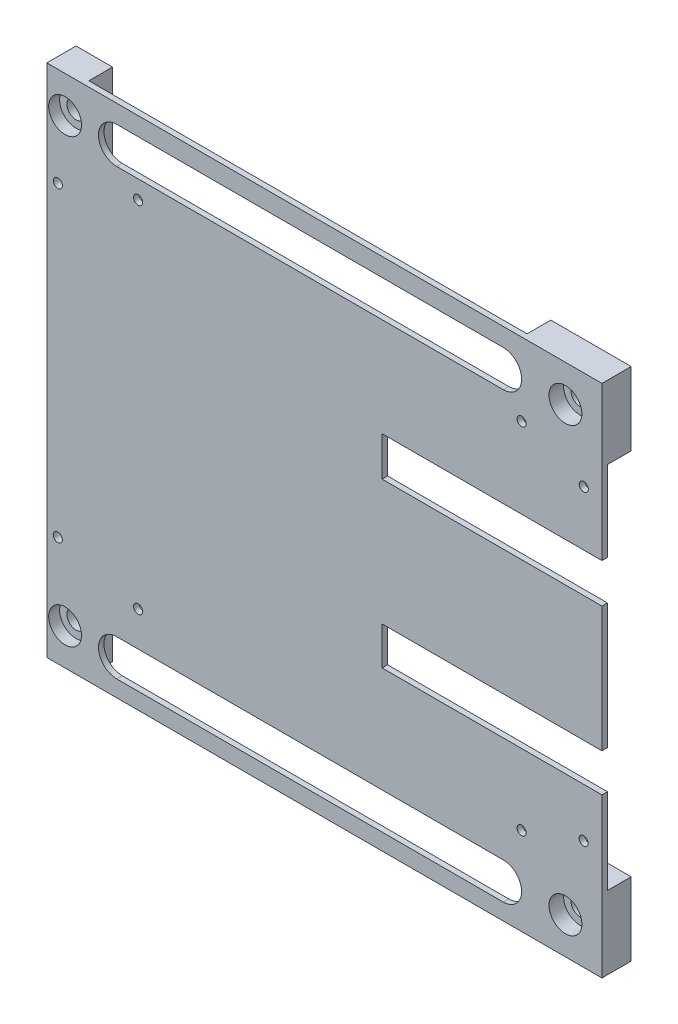
SolidWorks part; units mm, degrees
ref_plane "Front Plane" through (0, 0, 0) normal (0, 0, 1) x (1, 0, 0)
ref_plane "Top Plane" through (0, 0, 0) normal (0, 1, 0) x (1, 0, 0)
ref_plane "Right Plane" through (0, 0, 0) normal (1, 0, 0) x (0, 0, -1)
sketch "Sketch1" plane through (0, 0, 0) normal (0, 0, 1) x (1, 0, 0)
  line L0 (0, 0) -> (0, 141)
  line L1 (0, 141) -> (10, 141)
  line L2 (10, 141) -> (10, 0)
  line L3 (10, 0) -> (0, 0)
extrude "Boss-Extrude1" add sketch "Sketch1" along normal blind 8
sketch "Sketch2" plane through (0, 0, 8) normal (0, 0, 1) x (1, 0, 0)
  circle A0 centre (5, 131) radius 2.5
  circle A1 centre (5, 10) radius 2.5
extrude "Cut-Extrude1" cut sketch "Sketch2" against normal blind 8
sketch "Sketch3" plane through (0, 0, 8) normal (0, 0, 1) x (1, 0, 0)
  line L1 (10, 141) -> (152, 141)
  line L2 (10, 141) -> (10, 0)
  line L3 (10, 0) -> (152, 0)
  line L4 (152, 141) -> (152, 0)
extrude "Boss-Extrude2" add sketch "Sketch3" against normal blind 1.5
sketch "Sketch8" plane through (0, 0, 8) normal (0, 0, 1) x (1, 0, 0)
  line L0 (19.1432, 131) -> (125, 131) construction
  line L1 (19.1432, 136) -> (125, 136)
  line L2 (19.1432, 126) -> (125, 126)
  line L3 (19.1432, 9.4959) -> (125, 9.4959) construction
  line L4 (19.1432, 14.4959) -> (125, 14.4959)
  line L5 (19.1432, 4.4959) -> (125, 4.4959)
  arc A0 (19.1432, 136) -> (19.1432, 126) centre (19.1432, 131) ccw
  arc A1 (125, 126) -> (125, 136) centre (125, 131) ccw
  arc A2 (19.1432, 14.4959) -> (19.1432, 4.4959) centre (19.1432, 9.4959) ccw
  arc A3 (125, 4.4959) -> (125, 14.4959) centre (125, 9.4959) ccw
  point P3 (72.0716, 131)
  point P8 (125, 131)
  point P9 (0, 0)
  point P13 (72.0716, 9.4959)
  point P21 (0, 0)
  point P22 (125, 9.8292)
extrude "Cut-Extrude4" cut sketch "Sketch8" against normal blind 24
sketch "Sketch9" plane through (0, 0, 8) normal (0, 0, 1) x (1, 0, 0)
  circle A3 centre (147.0288, 114.0076) radius 1.25
  circle A4 centre (3.0274, 114) radius 1.25
  circle A5 centre (3, 30.0194) radius 1.25
  circle A6 centre (147, 30.0194) radius 1.25
sketch "Sketch12" plane through (0, 0, 8) normal (0, 0, 1) x (1, 0, 0)
  line L0 (151.8, -119) -> (151.8, 141) construction
  line L1 (151.8, 98.9737) -> (91.8, 98.9737)
  line L2 (151.8, 98.9737) -> (151.8, 88.196)
  line L3 (151.8, 88.196) -> (91.8, 88.196)
  line L4 (91.8, 98.9737) -> (91.8, 88.196)
  line L6 (151.8, 53.8659) -> (91.8, 53.8659)
  line L7 (151.8, 53.8659) -> (151.8, 43.4296)
  line L8 (151.8, 43.4296) -> (91.8, 43.4296)
  line L9 (91.8, 53.8659) -> (91.8, 43.4296)
  point P10 (0, 0)
  point P11 (0, 0)
extrude "Cut-Extrude6" cut sketch "Sketch12" against normal blind 10
sketch "Sketch13" plane through (0, 0, 8) normal (0, 0, 1) x (1, 0, 0)
  circle A0 centre (142, 131) radius 2.5
  circle A1 centre (142, 10) radius 2.5
sketch "Sketch14" plane through (0, 0, 6.5) normal (0, 0, -1) x (-1, 0, 0)
  line L1 (-152, 141) -> (-130, 141)
  line L2 (-152, 141) -> (-152, 121)
  line L3 (-152, 121) -> (-130, 121)
  line L4 (-130, 141) -> (-130, 121)
  line L5 (-152, 0) -> (-130, 0)
  line L6 (-152, 0) -> (-152, 20)
  line L7 (-152, 20) -> (-130, 20)
  line L8 (-130, 0) -> (-130, 20)
extrude "Boss-Extrude5" add sketch "Sketch14" along normal blind 6.5
sketch "Sketch16" plane through (0, 0, 8) normal (0, 0, 1) x (1, 0, 0)
  line L1 (91.8, 98.9737) -> (153.1804, 98.9737)
  line L2 (91.8, 98.9737) -> (91.8, 88.196)
  line L3 (91.8, 88.196) -> (153.1804, 88.196)
  line L4 (153.1804, 98.9737) -> (153.1804, 88.196)
  line L5 (91.8, 53.8659) -> (153.1804, 53.8659)
  line L6 (91.8, 53.8659) -> (91.8, 43.425)
  line L7 (91.8, 43.425) -> (153.1804, 43.425)
  line L8 (153.1804, 53.8659) -> (153.1804, 43.425)
extrude "Cut-Extrude9" cut sketch "Sketch16" against normal blind 26.5
sketch "Sketch17" plane through (0, 0, 8) normal (0, 0, 1) x (1, 0, 0)
  circle A0 centre (5, 131) radius 4.5
  circle A3 centre (5, 10) radius 4.5
extrude "Cut-Extrude10" cut sketch "Sketch17" against normal blind 3
extrude "Cut-Extrude11" cut sketch "Sketch9" against normal blind 14
extrude "Cut-Extrude12" cut sketch "Sketch13" against normal blind 14
sketch "Sketch19" plane through (0, 0, 8) normal (0, 0, 1) x (1, 0, 0)
  circle A0 centre (142, 131) radius 4.5
  circle A1 centre (142, 10) radius 4.5
extrude "Cut-Extrude13" cut sketch "Sketch19" against normal blind 4
sketch "Sketch20" plane through (0, 0, 8) normal (0, 0, 1) x (1, 0, 0)
  circle A0 centre (25, 121) radius 1.25
  circle A1 centre (130, 121) radius 1.25
  circle A2 centre (130, 24) radius 1.25
  circle A3 centre (25, 24) radius 1.25
extrude "Cut-Extrude14" cut sketch "Sketch20" against normal blind 4
